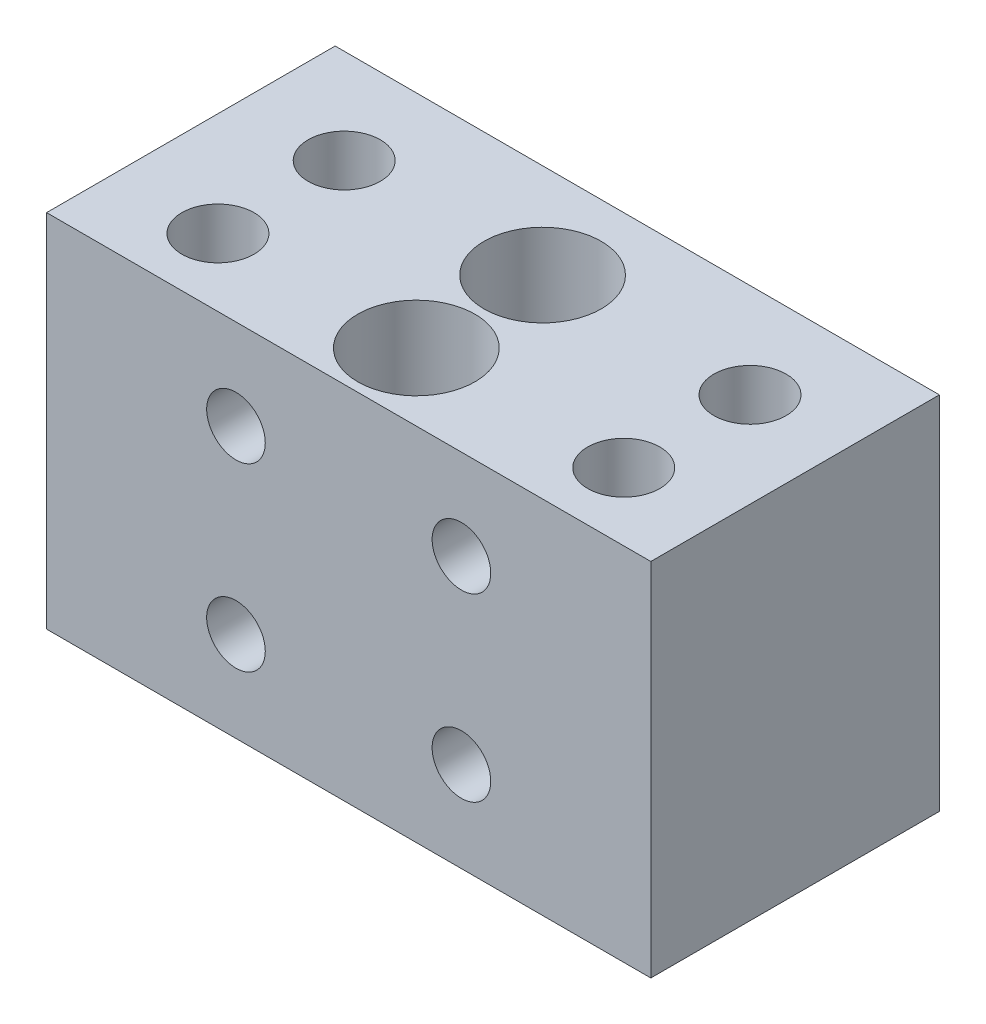
SolidWorks part; units mm, degrees
ref_plane "Front Plane" through (0, 0, 0) normal (0, 0, 1) x (1, 0, 0)
ref_plane "Top Plane" through (0, 0, 0) normal (0, 1, 0) x (1, 0, 0)
ref_plane "Right Plane" through (0, 0, 0) normal (1, 0, 0) x (0, 0, -1)
sketch "Sketch1" plane through (0, 0, 0) normal (0, 0, 1) x (1, 0, 0)
  line L1 (0, 0) -> (67, 0)
  line L2 (0, 0) -> (0, 40)
  line L3 (0, 40) -> (67, 40)
  line L4 (67, 0) -> (67, 40)
  dimension "D1" = 67
  dimension "D2" = 40
extrude "Boss-Extrude1" add sketch "Sketch1" along normal blind 32
sketch "Sketch2" plane through (0, 0, 0) normal (0, -1, 0) x (1, 0, 0)
  line L0 (0, 32) -> (67, 32) construction
  line L1 (0, 32) -> (0, 0) construction
  circle A0 centre (11.5, 24.5) radius 6
  dimension "D1" = 12
  dimension "D3" = 11.5
  dimension "D2" = 7.5
extrude "Cut-Extrude1" cut sketch "Sketch2" against normal blind 19
sketch "Sketch4" plane through (0, 19, 0) normal (0, -1, 0) x (1, 0, 0)
  circle A0 centre (11.5, 24.5) radius 4
  dimension "D1" = 8
extrude "Cut-Extrude2" cut sketch "Sketch4" against normal through all
pattern_linear "LPattern1" count 2 spacing 45 along (1, 0, 0) count 2 spacing 14 along (0, 0, -1) of "Cut-Extrude1", "Cut-Extrude2"
sketch "Sketch5" plane through (0, 40, 0) normal (0, 1, 0) x (1, 0, 0)
  line L0 (67, 0) -> (0, 0) construction
  line L1 (67, -32) -> (0, -32) construction
  circle A0 centre (33.5, -10.5) radius 6.5
  circle A1 centre (33.5, -24.5) radius 6.5
  point P7 (33.5, 0)
  dimension "D1" = 13
  dimension "D2" = 14
  dimension "D3" = 7.5
extrude "Cut-Extrude3" cut sketch "Sketch5" against normal blind 35
hole_wizard "M4x0.7 Tapped Hole1" positions "Sketch7" profile "Sketch8" tap size "M4x0.7" standard "ANSI Metric" end condition through all
sketch "Sketch7" plane through (0, 5, 0) normal (0, 1, 0) x (1, 0, 0)
  point P2 (33.5, -24.5)
  point P14 (33.5, -10.5)
sketch "Sketch8" plane through (33.5, 5, 24.5) normal (1, 0, 0) x (0, 0, 1)
  line L0 (0, 0) -> (0, 5)
  line L1 (0, 5) -> (1.65, 5)
  line L2 (1.65, 5) -> (1.65, 0)
  line L5 (1.65, 0) -> (0, 0)
  line L11 (0, -6.35) -> (0, 107.95) construction
  dimension "Thru Tap Drill Dia." = 3.3
  dimension "Thru Tap Drill Depth" = 5
cosmetic thread "Hole Thread1" parameters "D2"=4
cosmetic thread "Hole Thread2" parameters "D2"=4
hole_wizard "CBORE for M3 SHCS1" positions "Sketch10" profile "Sketch9" counterbore size "M3" standard "ANSI Metric" end condition through all
sketch "Sketch10" plane through (0, 0, 32) normal (0, 0, 1) x (1, 0, 0)
  line L0 (67, 40) -> (0, 40) construction
  line L2 (0, 40) -> (0, 0) construction
  point P0 (21, 30)
  dimension "D1" = 10
  dimension "D2" = 21
sketch "Sketch9" plane through (21, 30, 32) normal (1, 0, 0) x (0, -1, 0)
  line L0 (0, 0) -> (0, 32)
  line L1 (0, 32) -> (1.7, 32)
  line L3 (1.7, 32) -> (1.7, 30)
  line L4 (1.7, 30) -> (3.25, 30)
  line L5 (3.25, 30) -> (3.25, 0)
  line L7 (3.25, 0) -> (0, 0)
  line L11 (0, -6.35) -> (0, 107.95) construction
  dimension "Thru Hole Dia." = 3.4
  dimension "Thru Hole Depth" = 32
  dimension "C'Bore Dia." = 6.5
  dimension "C'Bore Depth" = 30
pattern_linear "LPattern2" count 2 spacing 25 along (1, 0, 0) count 2 spacing 20 along (0, -1, 0) of "CBORE for M3 SHCS1"
hole_wizard "M3x0.5 Tapped Hole1" positions "Sketch11" profile "Sketch12" tap size "M3x0.5" standard "ANSI Metric"
sketch "Sketch11" plane through (0, 0, 0) normal (0, -1, 0) x (-1, 0, 0)
  line L0 (0, 0) -> (-67, 0) construction
  line L1 (-67, -32) -> (-67, 0) construction
  point P0 (-45.5, -17.5)
  point P2 (-21.5, -17.5)
  dimension "D1" = 17.5
  dimension "D2" = 21.5
  dimension "D3" = 24
cosmetic thread "Hole Thread3" parameters "D1"=4, "D2"=3
cosmetic thread "Hole Thread4" parameters "D1"=4, "D2"=3
sketch "Sketch12" plane through (45.5, 0, 17.5) normal (1, 0, 0) x (0, 0, -1)
  line L0 (0, 0) -> (0, 6.2511)
  line L1 (0, 6.2511) -> (1.25, 5.5)
  line L2 (1.25, 5.5) -> (1.25, 0)
  line L5 (1.25, 0) -> (0, 0)
  line L10 (0, 6.2511) -> (-1.25, 5.5) construction
  line L11 (0, -6.35) -> (0, 107.95) construction
  dimension "Tap Drill Dia." = 2.5
  dimension "Tap Drill Depth" = 5.5
  dimension "Drill Angle" = 118
